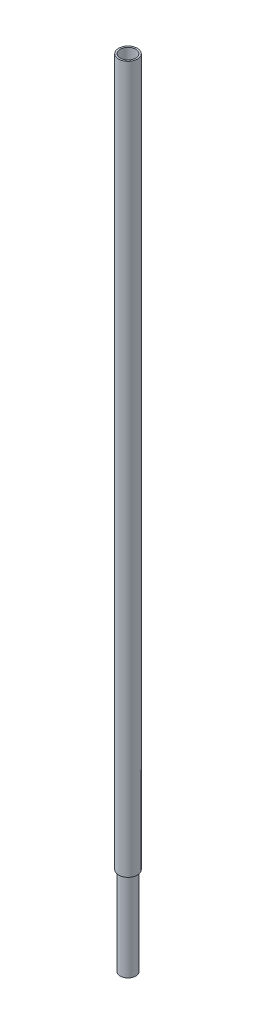
SolidWorks part; units mm, degrees
ref_plane "前视基准面" through (0, 0, 0) normal (0, 0, 1) x (1, 0, 0)
ref_plane "上视基准面" through (0, 0, 0) normal (0, 1, 0) x (1, 0, 0)
ref_plane "右视基准面" through (0, 0, 0) normal (1, 0, 0) x (0, 0, -1)
sketch "草图1" plane through (0, 0, 0) normal (0, 1, 0) x (1, 0, 0)
  circle A0 centre (0, 0) radius 4.25
  dimension "D1" = 8.5
extrude "凸台-拉伸1" add sketch "草图1" along normal blind 320
sketch "草图2" plane through (0, 0, 0) normal (0, 1, 0) x (1, 0, 0)
  circle A0 centre (0, 0) radius 3.5
  dimension "D1" = 7
extrude "切除-拉伸1" cut sketch "草图2" along normal blind 494
sketch "草图3" plane through (0, 0, 0) normal (0, 1, 0) x (1, 0, 0)
  circle A0 centre (0, 0) radius 3.5
  circle A1 centre (0, 0) radius 2.5
  dimension "D1" = 7
  dimension "D2" = 5
extrude "凸台-拉伸2" add sketch "草图3" along normal mid plane 80
